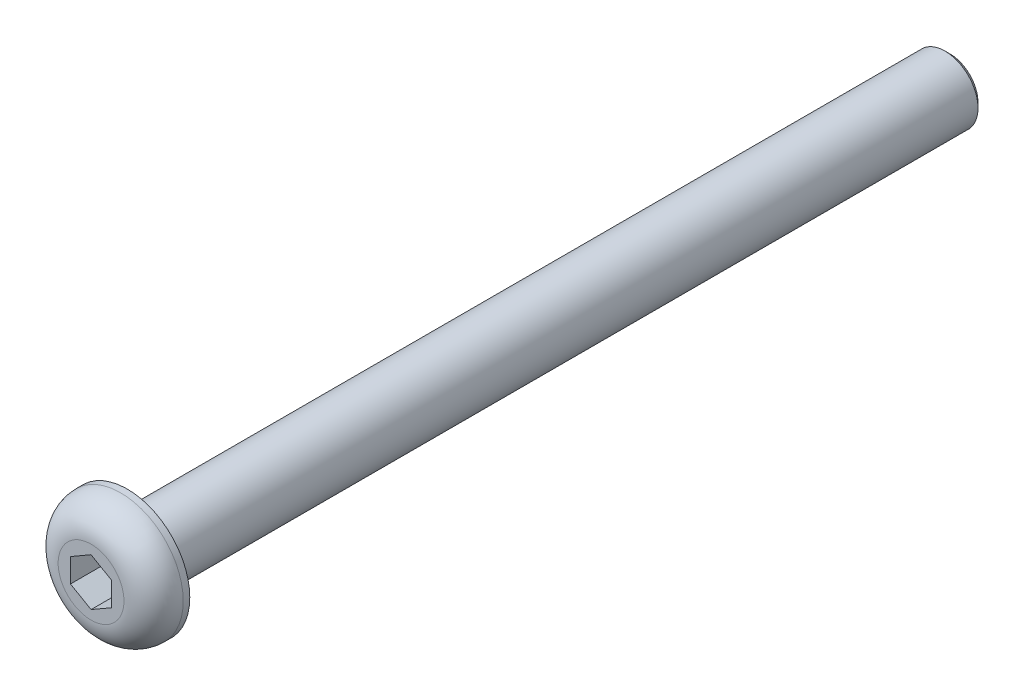
SolidWorks part; units mm, degrees
ref_plane "Front Plane" through (0, 0, 0) normal (0, 0, 1) x (1, 0, 0)
ref_plane "Top Plane" through (0, 0, 0) normal (0, 1, 0) x (1, 0, 0)
ref_plane "Right Plane" through (0, 0, 0) normal (1, 0, 0) x (0, 0, -1)
sketch "Sketch1" plane through (0, 0, 0) normal (0, 0, 1) x (1, 0, 0)
  circle A0 centre (0, 0) radius 3.8
  dimension "D1" = 7.6
extrude "Boss-Extrude1" add sketch "Sketch1" along normal blind 2.2
sketch "Sketch2" plane through (0, 0, 0) normal (0, 0, -1) x (-1, 0, 0)
  circle A0 centre (0, 0) radius 2
  dimension "D1" = 4
extrude "Boss-Extrude2" add sketch "Sketch2" along normal blind 50
chamfer "Chamfer1" distance 0.3 angle 45 1 edges at (-2, 0, -50)
sketch "Sketch3" plane through (0, 0, 2.2) normal (0, 0, 1) x (1, 0, 0)
  line L1 (0, 1.4434) -> (-1.25, 0.7217)
  line L2 (-1.25, 0.7217) -> (-1.25, -0.7217)
  line L3 (-1.25, -0.7217) -> (0, -1.4434)
  line L4 (0, -1.4434) -> (1.25, -0.7217)
  line L5 (1.25, -0.7217) -> (1.25, 0.7217)
  line L6 (1.25, 0.7217) -> (0, 1.4434)
  circle A0 centre (0, 0) radius 1.25 construction
  dimension "D1" = 2.5
extrude "Cut-Extrude1" cut sketch "Sketch3" against normal blind 2
fillet "Fillet1" radius 1.8 1 edges at (3.8, 0, 2.2)
